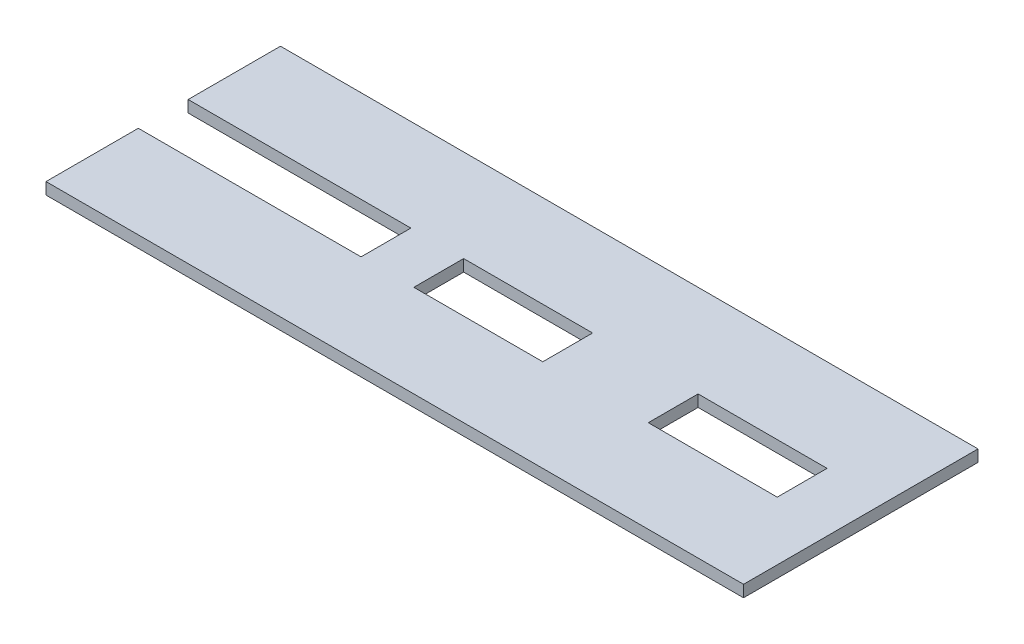
SolidWorks part; units mm, degrees
ref_plane "Front Plane" through (0, 0, 0) normal (0, 0, 1) x (1, 0, 0)
ref_plane "Top Plane" through (0, 0, 0) normal (0, 1, 0) x (1, 0, 0)
ref_plane "Right Plane" through (0, 0, 0) normal (1, 0, 0) x (0, 0, -1)
sketch "Sketch1" plane through (0, 0, 0) normal (0, 1, 0) x (1, 0, 0)
  line L1 (0, 0) -> (119, 0)
  line L2 (0, 0) -> (0, -40)
  line L3 (0, -40) -> (119, -40)
  line L4 (119, 0) -> (119, -40)
  dimension "D1" = 40
  dimension "D2" = 119
extrude "Boss-Extrude1" add sketch "Sketch1" along normal blind 2
sketch "Sketch2" plane through (0, 2, 0) normal (0, 1, 0) x (1, 0, 0)
  line L0 (0, -20) -> (119, -20) construction
  line L1 (0, 0) -> (0, -40) construction
  line L2 (119, -40) -> (119, 0) construction
  line L4 (0, -24.25) -> (38, -24.25)
  line L5 (0, -24.25) -> (0, -15.75)
  line L6 (0, -15.75) -> (38, -15.75)
  line L7 (38, -24.25) -> (38, -15.75)
  point P10 (0, -20)
  dimension "D1" = 38
  dimension "D2" = 8.5
extrude "Cut-Extrude1" cut sketch "Sketch2" against normal through all
sketch "Sketch3" plane through (0, 2, 0) normal (0, 1, 0) x (1, 0, 0)
  line L0 (119, -20) -> (0, -20) construction
  line L1 (119, -40) -> (119, 0) construction
  line L2 (0, 0) -> (0, -15.75) construction
  line L3 (47, -15.75) -> (69, -15.75)
  line L4 (47, -15.75) -> (47, -24.25)
  line L5 (47, -24.25) -> (69, -24.25)
  line L6 (69, -15.75) -> (69, -24.25)
  line L8 (87, -15.75) -> (109, -15.75)
  line L9 (87, -15.75) -> (87, -24.25)
  line L10 (87, -24.25) -> (109, -24.25)
  line L11 (109, -15.75) -> (109, -24.25)
  point P8 (47, -20)
  point P11 (58, -15.75)
  point P16 (87, -20)
  point P17 (98, -15.75)
  dimension "D1" = 58
  dimension "D2" = 8.5
  dimension "D3" = 22
  dimension "D4" = 40
  dimension "D5" = 22
  dimension "D6" = 8.5
extrude "Cut-Extrude2" cut sketch "Sketch3" against normal through all
equation "\"D6@Sketch3\"=\"D2@Sketch3\""
equation "\"D5@Sketch3\"=\"D3@Sketch3\""
